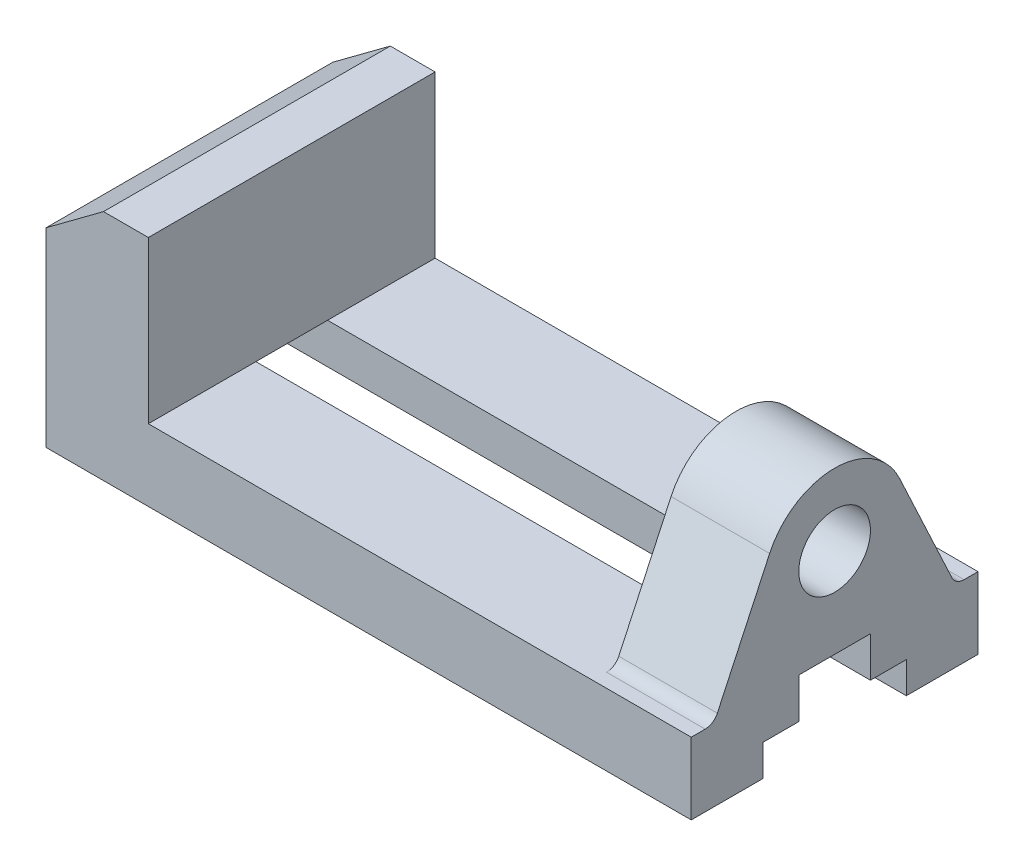
SolidWorks part; units mm, degrees
ref_plane "Front Plane" through (0, 0, 0) normal (0, 0, 1) x (1, 0, 0)
ref_plane "Top Plane" through (0, 0, 0) normal (0, 1, 0) x (1, 0, 0)
ref_plane "Right Plane" through (0, 0, 0) normal (1, 0, 0) x (0, 0, -1)
sketch "Sketch3" plane through (0, 0, 0) normal (0, 0, 1) x (1, 0, 0)
  line L0 (0, 0) -> (0, 42.4529)
  line L1 (0, 42.4529) -> (12.8395, 52)
  line L2 (12.8395, 52) -> (22.8395, 52)
  line L3 (22.8395, 52) -> (22.8395, 16)
  line L4 (22.8395, 16) -> (144, 16)
  line L5 (144, 16) -> (144, 0)
  line L6 (144, 0) -> (0, 0)
  dimension "D1" = 144
  dimension "D2" = 16
  dimension "D3" = 10
  dimension "D4" = 16
  dimension "D5" = 36
extrude "Boss-Extrude1" add sketch "Sketch3" along normal mid plane 64
sketch "Sketch5" plane through (144, 0, 0) normal (1, 0, 0) x (0, 0, -1)
  line L1 (-14.5009, 42.7619) -> (-26.1725, 17.7321)
  line L2 (14.5009, 42.7619) -> (26.1725, 17.7321)
  line L3 (-32, 16) -> (32, 16) construction
  line L4 (-32, 16) -> (-28.8914, 16)
  line L5 (-32, 16) -> (32, 16) construction
  line L6 (28.8914, 16) -> (32, 16)
  line L7 (-28.8914, 16) -> (28.8914, 16)
  circle A0 centre (0, 36) radius 16
  circle A1 centre (0, 36) radius 8
  arc A2 (-28.8914, 16) -> (-26.1725, 17.7321) centre (-28.8914, 19) ccw
  arc A3 (28.8914, 16) -> (26.1725, 17.7321) centre (28.8914, 19) cw
  dimension "D1" = 16
  dimension "D4" = 3
  dimension "D5" = 3
  dimension "D6" = 50
extrude "Boss-Extrude2" add sketch "Sketch5" against normal blind 22
sketch "Sketch8" plane through (144, 0, 0) normal (1, 0, 0) x (0, 0, -1)
  line L0 (-16, 0) -> (-16, 7)
  line L1 (-32, 0) -> (32, 0) construction
  line L2 (-16, 7) -> (-8, 7)
  line L3 (-8, 7) -> (-8, 16)
  line L4 (-8, 16) -> (8, 16)
  line L5 (8, 16) -> (8, 7)
  line L6 (8, 7) -> (16, 7)
  line L7 (16, 7) -> (16, 0)
  line L8 (16, 0) -> (-16, 0)
  dimension "D1" = 32
  dimension "D2" = 16
  dimension "D3" = 16
  dimension "D4" = 8
  dimension "D5" = 7
  dimension "D6" = 16
  dimension "D7" = 7
extrude "Cut-Extrude1" cut sketch "Sketch8" against normal up to next
sketch "Sketch9" plane through (0, 0, 0) normal (0, -1, 0) x (1, 0, 0)
  line L0 (0, 32) -> (144, 32) construction
  line L1 (0, 32) -> (0, 16) construction
  circle A0 centre (38, 22) radius 3
  dimension "D1" = 6
  dimension "D2" = 10
  dimension "D3" = 38
extrude "Cut-Extrude2" cut sketch "Sketch9" against normal blind 10
pattern_linear "LPattern1" count 2 spacing 70 along (1, 0, 0) count 2 spacing 44 along (0, 0, -1) of "Cut-Extrude2"
